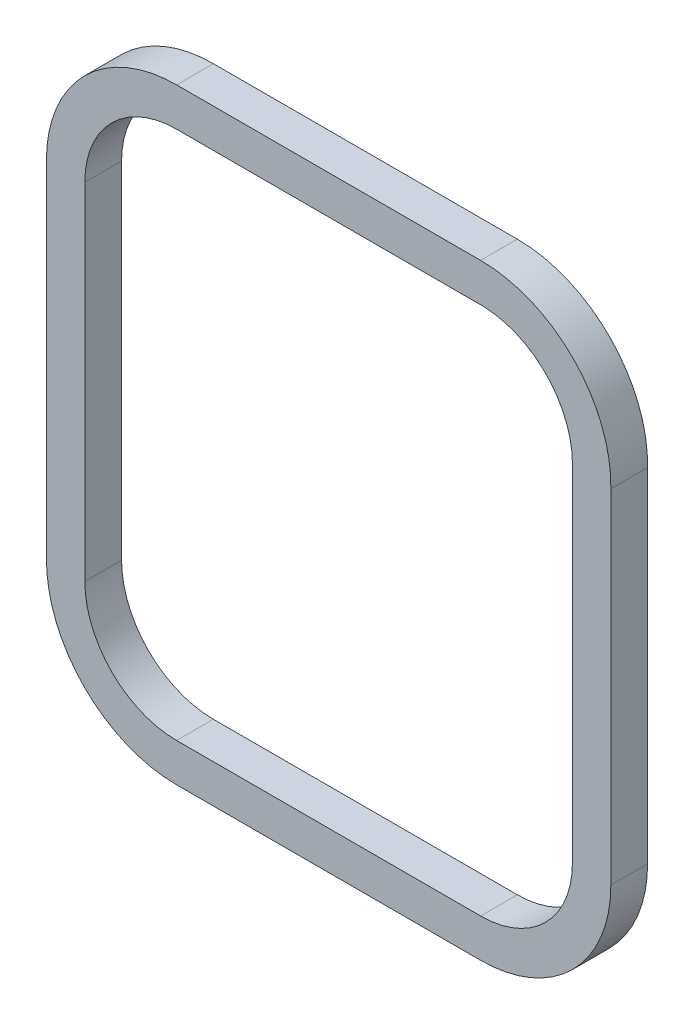
SolidWorks part; units mm, degrees
ref_plane "Front Plane" through (0, 0, 0) normal (0, 0, 1) x (1, 0, 0)
ref_plane "Top Plane" through (0, 0, 0) normal (0, 1, 0) x (1, 0, 0)
ref_plane "Right Plane" through (0, 0, 0) normal (1, 0, 0) x (0, 0, -1)
sketch "Sketch1" plane through (0, 0, 0) normal (0, 0, 1) x (1, 0, 0)
  line L0 (-15.85, 10.35) -> (-15.85, -10.35)
  line L1 (-18.15, 10.35) -> (-18.15, -10.35)
  line L2 (-10.35, -18.15) -> (7.85, -18.15)
  line L3 (-10.35, -15.85) -> (7.85, -15.85)
  line L4 (15.65, -10.35) -> (15.65, 10.202)
  line L6 (13.35, -10.35) -> (13.35, 10.35)
  line L7 (-10.3489, 15.85) -> (8.0531, 15.8462)
  line L8 (-10.35, 18.15) -> (7.85, 18.15)
  line L9 (0, 0) -> (25.3121, 0) construction
  line L10 (0, 0) -> (0, 21.7943) construction
  arc A0 (-15.85, 10.35) -> (-10.3489, 15.85) centre (-10.35, 10.35) cw
  arc A1 (8.0531, 15.8462) -> (13.35, 10.35) centre (7.85, 10.35) cw
  arc A2 (-15.85, -10.35) -> (-10.35, -15.85) centre (-10.35, -10.35) ccw
  arc A3 (7.85, -15.85) -> (13.35, -10.35) centre (7.85, -10.35) ccw
  arc A4 (7.85, 18.15) -> (15.65, 10.202) centre (7.8514, 10.35) cw
  arc A5 (-18.15, 10.35) -> (-10.35, 18.15) centre (-10.35, 10.35) cw
  arc A6 (15.65, -10.35) -> (7.85, -18.15) centre (7.85, -10.35) cw
  arc A7 (-18.15, -10.35) -> (-10.35, -18.15) centre (-10.35, -10.35) ccw
  point P28 (0, 0)
extrude "Boss-Extrude1" add sketch "Sketch1" along normal blind 2.2
